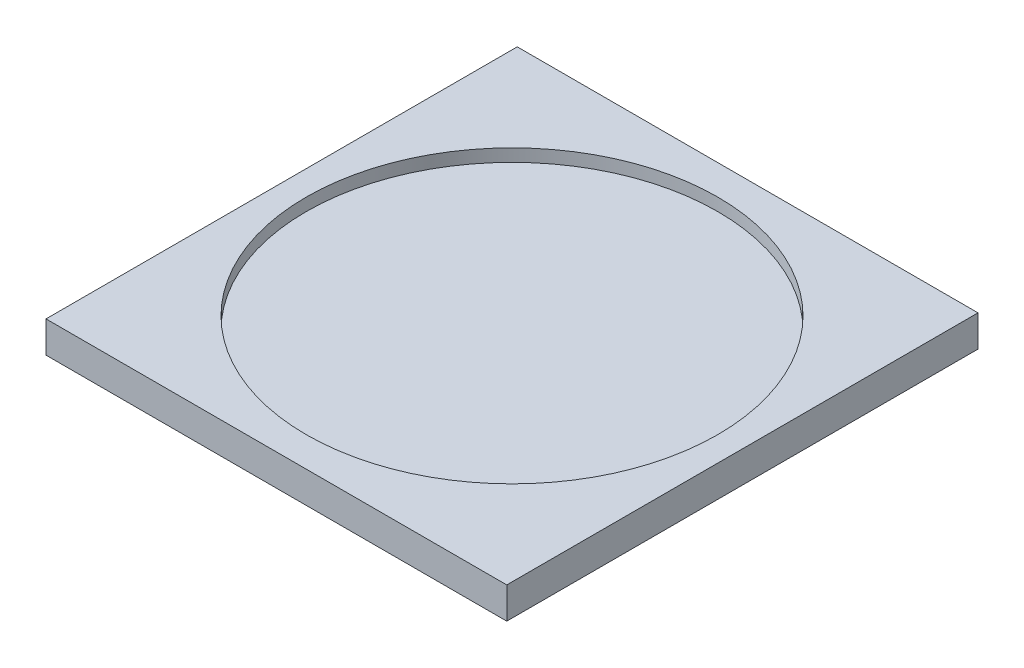
SolidWorks part; units mm, degrees
ref_plane "Front Plane" through (0, 0, 0) normal (0, 0, 1) x (1, 0, 0)
ref_plane "Top Plane" through (0, 0, 0) normal (0, 1, 0) x (1, 0, 0)
ref_plane "Right Plane" through (0, 0, 0) normal (1, 0, 0) x (0, 0, -1)
sketch "Sketch1" plane through (0, 0, 0) normal (0, 1, 0) x (1, 0, 0)
  line L1 (0, 0) -> (-73.3333, 0)
  line L2 (0, 0) -> (0, 75)
  line L3 (0, 75) -> (-73.3333, 75)
  line L4 (-73.3333, 0) -> (-73.3333, 75)
  dimension "D1" = 73.3333
  dimension "D2" = 75
extrude "Boss-Extrude1" add sketch "Sketch1" along normal blind 5
sketch "Sketch2" plane through (0, 5, 0) normal (0, 1, 0) x (1, 0, 0)
  line L0 (-36.6667, 75) -> (-36.6667, 0) construction
  line L1 (0, 75) -> (-73.3333, 75) construction
  line L2 (-73.3333, 0) -> (0, 0) construction
  circle A0 centre (-36.6667, 37.5) radius 32.75
  dimension "D1" = 65.5
extrude "Cut-Extrude1" cut sketch "Sketch2" against normal blind 2
